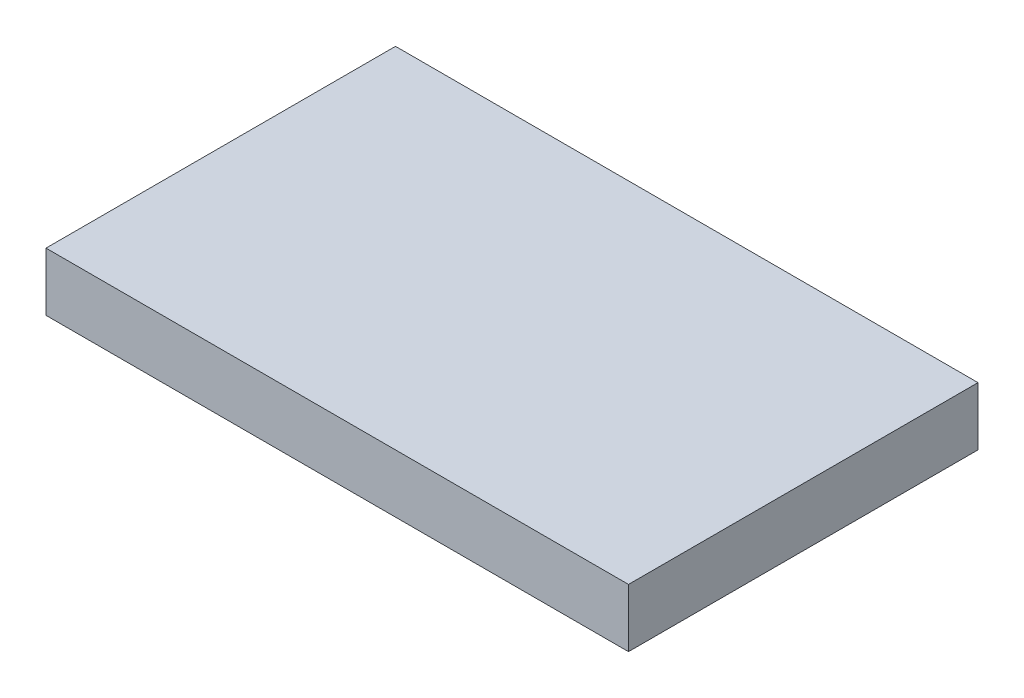
SolidWorks part; units mm, degrees
ref_plane "Front Plane" through (0, 0, 0) normal (0, 0, 1) x (1, 0, 0)
ref_plane "Top Plane" through (0, 0, 0) normal (0, 1, 0) x (1, 0, 0)
ref_plane "Right Plane" through (0, 0, 0) normal (1, 0, 0) x (0, 0, -1)
sketch "Sketch1" plane through (0, 0, 0) normal (0, 1, 0) x (1, 0, 0)
  line L1 (0, 0) -> (47.625, 0)
  line L2 (0, 0) -> (0, -28.575)
  line L3 (0, -28.575) -> (47.625, -28.575)
  line L4 (47.625, 0) -> (47.625, -28.575)
  dimension "D1" = 28.575
  dimension "D2" = 47.625
extrude "Boss-Extrude1" add sketch "Sketch1" along normal blind 4.7625
